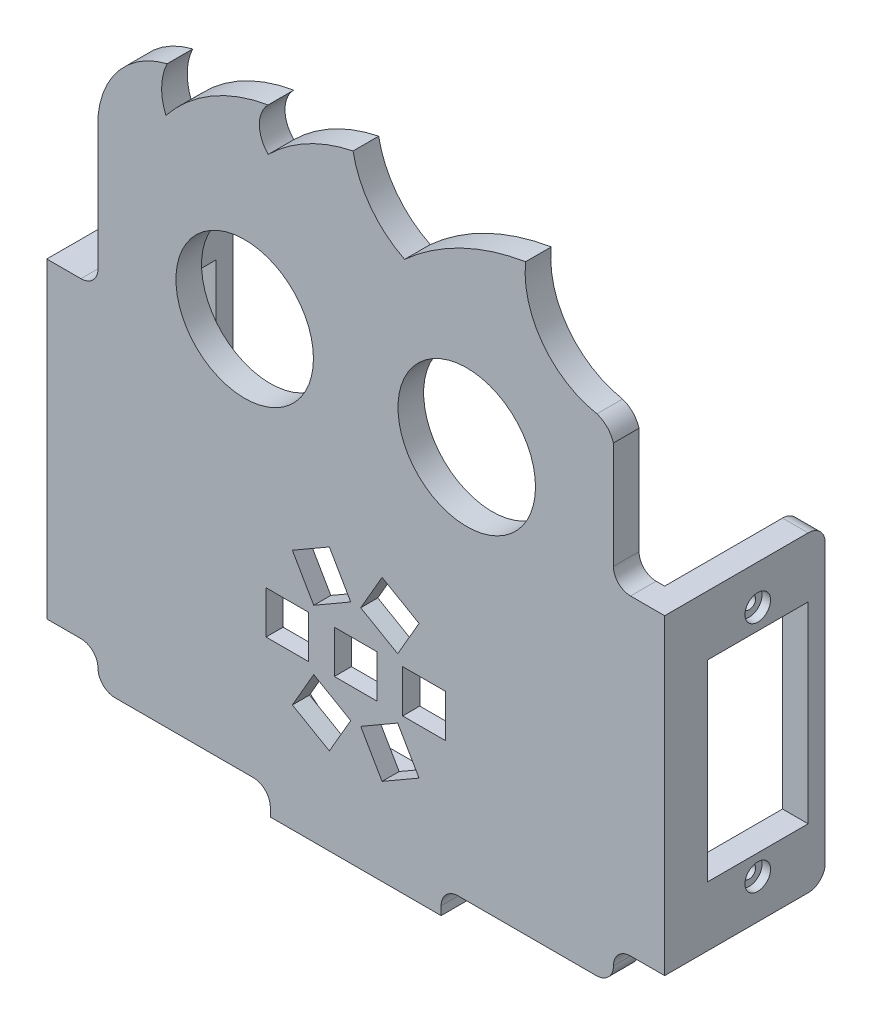
SolidWorks part; units mm, degrees
ref_plane "Alzado" through (0, 0, 0) normal (0, 0, 1) x (1, 0, 0)
ref_plane "Planta" through (0, 0, 0) normal (0, 1, 0) x (1, 0, 0)
ref_plane "Vista lateral" through (0, 0, 0) normal (1, 0, 0) x (0, 0, -1)
sketch "Model" plane through (0, 0, 0) normal (0, 0, 1) x (1, 0, 0)
  line L0 (24.5271, -12.521) -> (24.5271, -49.021)
  line L1 (50.699, -56.021) -> (70.699, -56.021)
  line L2 (60.699, -38.021) -> (60.699, -56.021) construction
  line L3 (32.5271, -53.021) -> (48.699, -53.021)
  line L4 (88.8708, -53.021) -> (72.699, -53.021)
  line L5 (96.8708, -12.521) -> (92.8708, -12.521)
  line L6 (92.8708, -49.021) -> (96.8708, -49.021)
  line L7 (96.8708, -12.521) -> (96.8708, -49.021)
  line L8 (90.8708, 1.9881) -> (90.8708, -10.521)
  line L9 (30.5271, 4.9744) -> (30.5271, -10.521)
  line L42 (58.199, -33.021) -> (58.199, -38.021)
  line L43 (58.199, -38.021) -> (63.199, -38.021)
  line L44 (63.199, -38.021) -> (63.199, -33.021)
  line L45 (63.199, -33.021) -> (58.199, -33.021)
  line L46 (50.199, -33.021) -> (50.199, -38.021)
  line L47 (50.199, -38.021) -> (55.199, -38.021)
  line L48 (55.199, -38.021) -> (55.199, -33.021)
  line L49 (55.199, -33.021) -> (50.199, -33.021)
  line L50 (57.614, -25.1777) -> (53.2839, -27.6777)
  line L51 (53.2839, -27.6777) -> (55.7839, -32.0079)
  line L52 (55.7839, -32.0079) -> (60.114, -29.5079)
  line L53 (60.114, -29.5079) -> (57.614, -25.1777)
  line L54 (68.114, -27.6777) -> (63.7839, -25.1777)
  line L55 (63.7839, -25.1777) -> (61.2839, -29.5079)
  line L56 (61.2839, -29.5079) -> (65.614, -32.0079)
  line L57 (65.614, -32.0079) -> (68.114, -27.6777)
  line L58 (71.199, -38.021) -> (71.199, -33.021)
  line L59 (71.199, -33.021) -> (66.199, -33.021)
  line L60 (66.199, -33.021) -> (66.199, -38.021)
  line L61 (66.199, -38.021) -> (71.199, -38.021)
  line L62 (63.7839, -45.8643) -> (68.114, -43.3643)
  line L63 (68.114, -43.3643) -> (65.614, -39.0341)
  line L64 (65.614, -39.0341) -> (61.2839, -41.5341)
  line L65 (61.2839, -41.5341) -> (63.7839, -45.8643)
  line L66 (53.2839, -43.3643) -> (57.614, -45.8643)
  line L67 (57.614, -45.8643) -> (60.114, -41.5341)
  line L68 (60.114, -41.5341) -> (55.7839, -39.0341)
  line L69 (55.7839, -39.0341) -> (53.2839, -43.3643)
  line L80 (70.699, -55.021) -> (70.699, -56.021)
  line L110 (50.699, -56.021) -> (50.699, -55.021)
  line L113 (28.5271, -49.021) -> (24.5271, -49.021)
  line L115 (24.5271, -12.521) -> (28.5271, -12.521)
  arc A0 (30.5271, -10.521) -> (28.5271, -12.521) centre (28.5271, -10.521) cw
  arc A1 (30.5271, -51.021) -> (28.5271, -49.021) centre (28.5271, -51.021) ccw
  arc A2 (90.8708, -51.021) -> (92.8708, -49.021) centre (92.8708, -51.021) cw
  arc A3 (90.8708, -10.521) -> (92.8708, -12.521) centre (92.8708, -10.521) ccw
  arc A4 (70.699, -55.021) -> (72.699, -53.021) centre (72.699, -55.021) cw
  arc A5 (50.699, -55.021) -> (48.699, -53.021) centre (48.699, -55.021) ccw
  circle A31 centre (73.699, -7.021) radius 8.05
  circle A32 centre (47.699, -7.021) radius 8.05
  arc A35 (38.6183, 14.3189) -> (30.5271, 4.9744) centre (41.1247, 3.9735) ccw
  arc A36 (38.6183, 14.3189) -> (38.4712, 8.9961) centre (44.4932, 11.4932) ccw
  arc A37 (50.4388, 16.0514) -> (38.4712, 8.9961) centre (53.6269, -3.0341) ccw
  arc A38 (50.4388, 16.0514) -> (50.4619, 11.0514) centre (52.9503, 13.5629) ccw
  arc A39 (60.3874, 16.3614) -> (50.4619, 11.0514) centre (64.38, -3.0332) ccw
  arc A40 (60.3874, 16.3614) -> (66.4243, 8.3891) centre (71.3781, 18.4121) ccw
  arc A41 (80.5924, 15.2365) -> (66.4243, 8.3891) centre (85.17, -12.3168) ccw
  arc A42 (80.5924, 15.2365) -> (88.9405, 3.9825) centre (90.8389, 14.114) ccw
  arc A43 (90.8708, 1.9881) -> (88.9405, 3.9825) centre (87.9945, 1.1356) ccw
  arc A48 (88.8708, -53.021) -> (90.8708, -51.021) centre (88.8708, -51.021) ccw
  arc A65 (30.5271, -51.021) -> (32.5271, -53.021) centre (32.5271, -51.021) ccw
  dimension "D1" = 2
  dimension "D2" = 2
  dimension "D4" = 2
  dimension "D5" = 26
  dimension "D3" = 20
extrude "Saliente-Extruir1" add sketch "Model" along normal blind 3
sketch "Croquis3" plane through (0, 0, 0) normal (0, 0, -1) x (-1, 0, 0)
  line L0 (-96.8708, -12.521) -> (-93.8708, -12.521)
  line L1 (-93.8708, -12.521) -> (-93.8708, -49.021)
  line L2 (-93.8708, -49.021) -> (-96.8708, -49.021)
  line L3 (-96.8708, -49.021) -> (-96.8708, -12.521)
  dimension "D1" = 3
extrude "Saliente-Extruir2" add sketch "Croquis3" along normal blind 15.8
sketch "Croquis4" plane through (96.8708, 0, 0) normal (1, 0, 0) x (0, 0, -1)
  line L0 (2, -19.521) -> (2, -42.021)
  line L1 (2, -42.021) -> (13.8, -42.021)
  line L2 (13.8, -42.021) -> (13.8, -19.521)
  line L3 (13.8, -19.521) -> (2, -19.521)
  line L4 (7.9, -44.421) -> (7.9, -17.121) construction
  line L5 (15.8, -12.521) -> (15.8, -49.021) construction
  line L6 (-3, -12.521) -> (15.8, -12.521) construction
  circle A0 centre (7.9, -44.421) radius 0.75
  circle A1 centre (7.9, -17.121) radius 0.75
  dimension "D1" = 2.4
  dimension "D2" = 11.8
  dimension "D3" = 22.5
  dimension "D4" = 2.4
  dimension "D5" = 5.9
  dimension "D6" = 2
  dimension "D7" = 7
extrude "Cortar-Extruir1" cut sketch "Croquis4" against normal blind 3
sketch "Croquis5" plane through (96.8708, 0, 0) normal (1, 0, 0) x (0, 0, -1)
  circle A0 centre (7.9, -17.121) radius 1.5
  circle A1 centre (7.9, -44.421) radius 1.5
extrude "Cortar-Extruir2" cut sketch "Croquis5" against normal blind 1
fillet "Redondeo1" radius 2 2 edges at (95.3708, -49.021, -15.8) (95.3708, -12.521, -15.8)
ref_plane "Plano1" through (60.7008, 0, 0) normal (1, 0, 0) x (0, 0, -1)
mirror "Simetría1" about plane through (60.7008, 0, 0) normal (1, 0, 0) of "Redondeo1", "Cortar-Extruir2", "Cortar-Extruir1", "Saliente-Extruir2"
sketch "Croquis6" plane through (0, 0, 0) normal (0, 0, -1) x (-1, 0, 0)
  line L0 (-70.699, -56.021) -> (-70.699, -53.021)
  line L1 (-70.699, -53.021) -> (-50.699, -53.021)
  line L2 (-50.699, -53.021) -> (-50.699, -56.021)
  line L3 (-50.699, -56.021) -> (-70.699, -56.021)
  dimension "D1" = 3
extrude "Saliente-Extruir3" add sketch "Croquis6" along normal blind 8
fillet "Redondeo2" radius 2 2 edges at (50.699, -54.521, -8) (70.699, -54.521, -8)
sketch "Croquis7" plane through (0, -53.021, 0) normal (0, 1, 0) x (1, 0, 0)
  line L0 (60.699, 8) -> (60.699, 0) construction
  line L1 (52.699, 8) -> (68.699, 8) construction
  line L2 (50.699, 0) -> (70.699, 0) construction
  circle A0 centre (66.699, 3.5) radius 1.5
  circle A1 centre (54.699, 3.5) radius 1.5
  dimension "D1" = 6
  dimension "D2" = 3.5
extrude "Cortar-Extruir3" cut sketch "Croquis7" against normal blind 3
sketch "Croquis8" plane through (0, -53.021, 0) normal (0, 1, 0) x (1, 0, 0)
  circle A0 centre (66.699, 3.5) radius 2.25
  circle A1 centre (54.699, 3.5) radius 2.25
extrude "Cortar-Extruir4" cut sketch "Croquis8" against normal blind 1
sketch "Croquis9" plane through (0, 0, 0) normal (0, 0, -1) x (-1, 0, 0)
  line L0 (-90.8708, -35.521) -> (-30.5271, -35.521) construction
  line L1 (-90.8708, -10.521) -> (-90.8708, 1.9881) construction
  line L2 (-30.5271, 4.9744) -> (-30.5271, -10.521) construction
  line L3 (-32.5271, -53.021) -> (-48.699, -53.021) construction
  circle A0 centre (-60.699, -35.521) radius 12
  dimension "D1" = 17.5
extrude "Cortar-Extruir5" cut sketch "Croquis9" against normal blind 1
